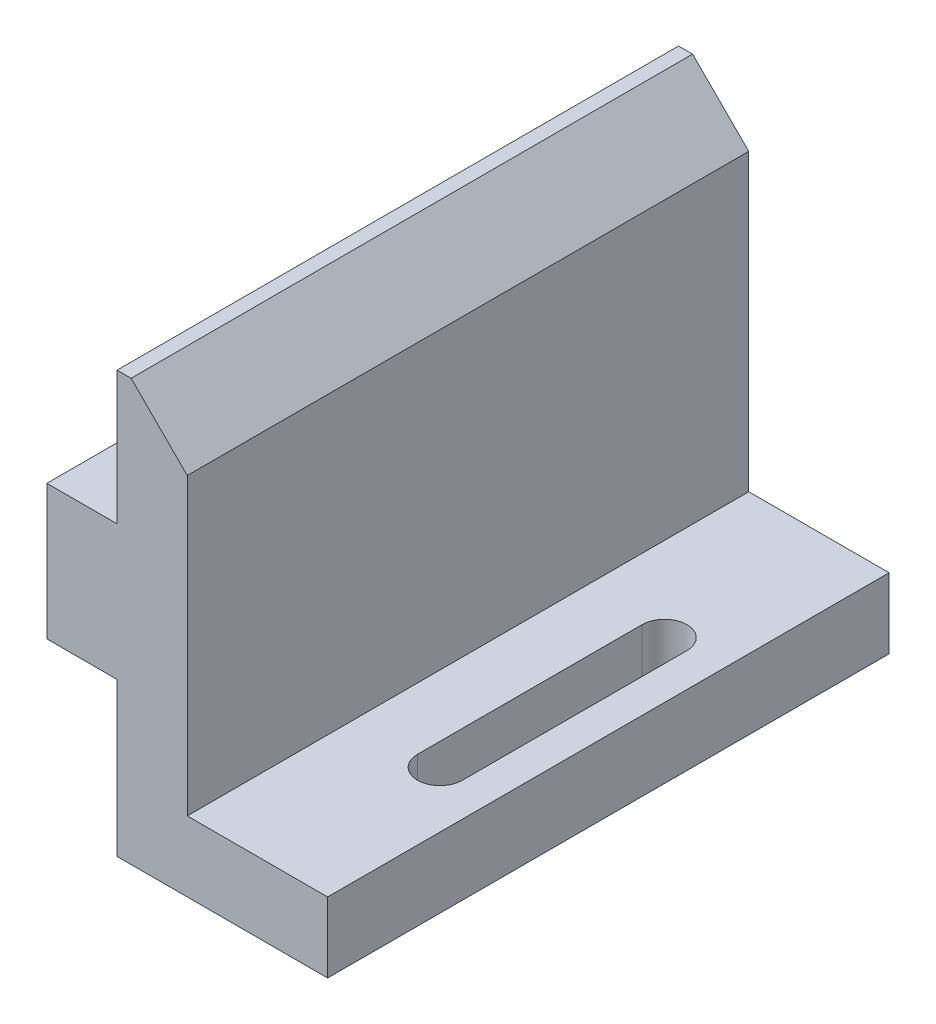
SolidWorks part; units mm, degrees
ref_plane "Front Plane" through (0, 0, 0) normal (0, 0, 1) x (1, 0, 0)
ref_plane "Top Plane" through (0, 0, 0) normal (0, 1, 0) x (1, 0, 0)
ref_plane "Right Plane" through (0, 0, 0) normal (1, 0, 0) x (0, 0, -1)
sketch "Sketch1" plane through (0, 0, 0) normal (0, 0, 1) x (1, 0, 0)
  line L0 (0, 0) -> (9.525, 0)
  line L1 (9.525, 0) -> (9.525, 3.175)
  line L2 (9.525, 3.175) -> (3.175, 3.175)
  line L3 (3.175, 3.175) -> (3.175, 19.05)
  line L4 (3.175, 19.05) -> (0, 19.05)
  line L5 (0, 19.05) -> (0, 0)
  dimension "D1" = 9.525
  dimension "D2" = 19.05
  dimension "D3" = 3.175
extrude "Boss-Extrude1" add sketch "Sketch1" along normal mid plane 25.4
sketch "Sketch2" plane through (0, 0, 0) normal (0, 0, 1) x (1, 0, 0)
  line L0 (0, 19.05) -> (0, 0) construction
  line L1 (0, 13.0302) -> (-3.175, 13.0302)
  line L2 (0, 13.0302) -> (0, 6.9342)
  line L3 (0, 6.9342) -> (-3.175, 6.9342)
  line L4 (-3.175, 13.0302) -> (-3.175, 6.9342)
  line L5 (0, 0) -> (9.525, 0) construction
  dimension "D1" = 6.096
  dimension "D2" = 3.175
  dimension "D3" = 6.9342
extrude "Boss-Extrude2" add sketch "Sketch2" along normal mid plane 25.4
sketch "Sketch3" plane through (0, 3.175, 0) normal (0, 1, 0) x (1, 0, 0)
  line L0 (6.985, 5.08) -> (6.985, -5.08) construction
  line L1 (8.001, 5.08) -> (8.001, -5.08)
  line L2 (5.969, 5.08) -> (5.969, -5.08)
  line L3 (9.525, -12.7) -> (9.525, 12.7) construction
  arc A0 (8.001, 5.08) -> (5.969, 5.08) centre (6.985, 5.08) ccw
  arc A1 (5.969, -5.08) -> (8.001, -5.08) centre (6.985, -5.08) ccw
  point P2 (6.985, 0)
  dimension "D3" = 1.016
  dimension "D1" = 2.54
  dimension "D2" = 10.16
extrude "Cut-Extrude1" cut sketch "Sketch3" against normal through all
chamfer "Chamfer1" distance 2.54 angle 45 1 edges at (3.175, 19.05, 0)
